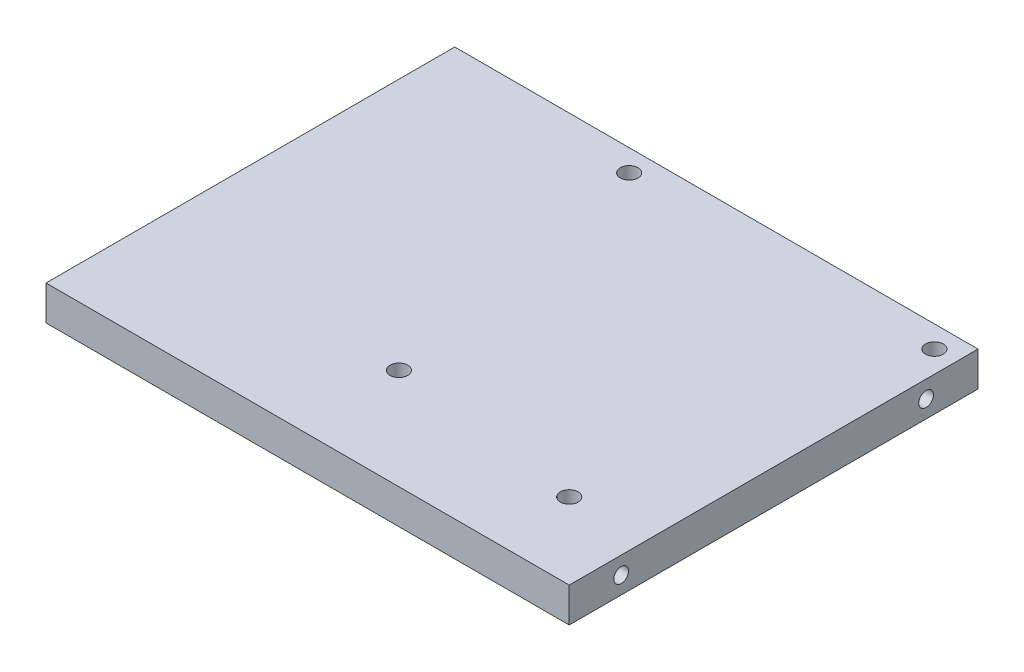
SolidWorks part; units mm, degrees
ref_plane "Front Plane" through (0, 0, 0) normal (0, 0, 1) x (1, 0, 0)
ref_plane "Top Plane" through (0, 0, 0) normal (0, 1, 0) x (1, 0, 0)
ref_plane "Right Plane" through (0, 0, 0) normal (1, 0, 0) x (0, 0, -1)
ref_plane "Plane1" through (0, -8, 0) normal (0, -1, 0) x (-1, 0, 0)
sketch "Sketch1" plane through (0, -8, 0) normal (0, -1, 0) x (-1, 0, 0)
  line L0 (0, 75) -> (0, 0) construction
  line L1 (0, 0) -> (-96, 0)
  line L2 (0, 0) -> (0, 75)
  line L3 (0, 75) -> (-96, 75)
  line L4 (-96, 0) -> (-96, 75)
  line L5 (4.7625, 75) -> (0, 75) construction
extrude "Boss-Extrude1" add sketch "Sketch1" against normal blind 6.35
sketch "Sketch2" plane through (0, -8, 0) normal (0, -1, 0) x (1, 0, 0)
  circle A0 centre (36, -71) radius 1.6319
  circle A1 centre (46.25, -18.5) radius 1.6319
  circle A2 centre (82, -14) radius 1.632
  circle A3 centre (92, -71) radius 1.6319
extrude "Cut-Extrude1" cut sketch "Sketch2" against normal blind 6.35
sketch "Sketch3" plane through (0, 0, 0) normal (-1, 0, 0) x (0, 0, 1)
  circle A0 centre (-65.475, -4.825) radius 1.3525
  circle A1 centre (-9.525, -4.825) radius 1.3526
  circle A2 centre (-9.525, -4.825) radius 1.8986 construction
  circle A3 centre (-65.475, -4.825) radius 1.8987 construction
extrude "Cut-Extrude2" cut sketch "Sketch3" against normal blind 9.525
sketch "Sketch4" plane through (96, 0, 0) normal (1, 0, 0) x (0, 0, -1)
  circle A0 centre (65.475, -4.825) radius 1.3525
  circle A1 centre (9.525, -4.825) radius 1.3526
  circle A2 centre (65.475, -4.825) radius 1.8987 construction
  circle A3 centre (9.525, -4.825) radius 1.8987 construction
extrude "Cut-Extrude3" cut sketch "Sketch4" against normal blind 9.525
